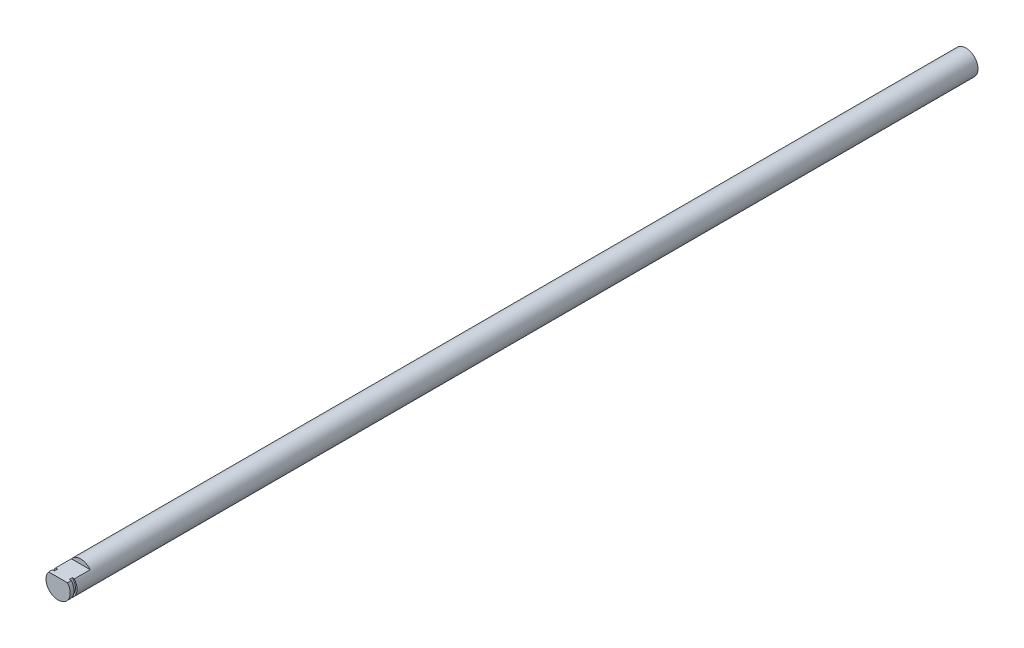
SolidWorks part; units mm, degrees
ref_plane "Front Plane" through (0, 0, 0) normal (0, 0, 1) x (1, 0, 0)
ref_plane "Top Plane" through (0, 0, 0) normal (0, 1, 0) x (1, 0, 0)
ref_plane "Right Plane" through (0, 0, 0) normal (1, 0, 0) x (0, 0, -1)
sketch "Sketch1" plane through (0, 0, 0) normal (0, 0, 1) x (1, 0, 0)
  circle A0 centre (0, 0) radius 4
  dimension "D1" = 8
extrude "Boss-Extrude1" add sketch "Sketch1" along normal blind 325
sketch "Sketch2" plane through (0, 0, 325) normal (0, 0, 1) x (1, 0, 0)
  line L0 (3.1225, 2.5) -> (-3.1225, 2.5)
  circle A1 centre (0, 0) radius 4
  arc A2 (3.1225, 2.5) -> (-3.1225, 2.5) centre (0, 0) ccw
  dimension "D2" = 2.5
  dimension "D1" = 0
extrude "Cut-Extrude1" cut sketch "Sketch2" against normal blind 7.5
ref_plane "Plane1" through (0, 0, 323.75) normal (0, 0, 1) x (1, 0, 0)
sketch "Sketch3" plane through (0, 0, 323.75) normal (0, 0, 1) x (1, 0, 0)
  circle A0 centre (0, 0) radius 4
  circle A1 centre (0, 0) radius 3.5
extrude "Cut-Extrude2" cut sketch "Sketch3" against normal blind 1
sketch "Sketch5" plane through (0, 0, 0) normal (0, 0, -1) x (-1, 0, 0)
  circle A1 centre (0, 0) radius 4
  circle A2 centre (0, 0) radius 4
  dimension "D1" = 0
extrude "Cut-Extrude3" cut sketch "Sketch5" against normal blind 65
sketch "Sketch6" plane through (0, 0, 65) normal (0, 0, -1) x (-1, 0, 0)
  circle A1 centre (0, 0) radius 4
  circle A2 centre (0, 0) radius 4
  dimension "D1" = 0
extrude "Boss-Extrude2" add sketch "Sketch6" along normal blind 13
sketch "Sketch7" plane through (0, 0, 52) normal (0, 0, -1) x (-1, 0, 0)
  circle A1 centre (0, 0) radius 4
  circle A2 centre (0, 0) radius 4
  dimension "D1" = 0
extrude "Boss-Extrude3" add sketch "Sketch7" along normal blind 10
sketch "Sketch8" plane through (0, 0, 42) normal (0, 0, -1) x (-1, 0, 0)
  circle A1 centre (0, 0) radius 4
  circle A2 centre (0, 0) radius 4
  dimension "D1" = 0
extrude "Boss-Extrude4" add sketch "Sketch8" along normal blind 40
sketch "Sketch9" plane through (0, 0, 2) normal (0, 0, -1) x (-1, 0, 0)
  circle A1 centre (0, 0) radius 4
  circle A2 centre (0, 0) radius 4
  dimension "D1" = 0
extrude "Cut-Extrude4" cut sketch "Sketch9" against normal blind 30
sketch "Sketch10" plane through (0, 0, 32) normal (0, 0, -1) x (-1, 0, 0)
  circle A0 centre (0, 0) radius 4 construction
  circle A1 centre (0, 0) radius 4
extrude "Cut-Extrude5" cut sketch "Sketch10" against normal blind 61
sketch "Sketch11" plane through (0, 0, 93) normal (0, 0, -1) x (-1, 0, 0)
  circle A1 centre (0, 0) radius 4
  circle A2 centre (0, 0) radius 4
  dimension "D1" = 0
extrude "Boss-Extrude5" add sketch "Sketch11" along normal blind 68
